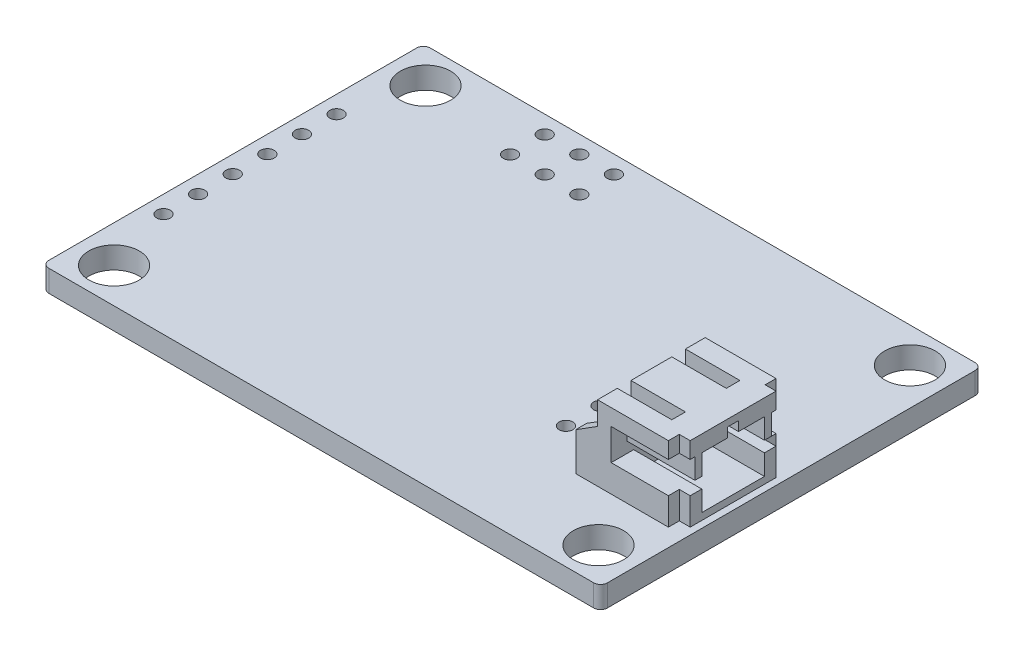
SolidWorks part; units mm, degrees
other "Sparkfun_board"
other "JST_connector"
ref_plane "Front Plane" through (0, 0, 0) normal (0, 0, 1) x (1, 0, 0)
ref_plane "Top Plane" through (0, 0, 0) normal (0, 1, 0) x (1, 0, 0)
ref_plane "Right Plane" through (0, 0, 0) normal (1, 0, 0) x (0, 0, -1)
sketch "dimension" plane through (0, 0, 0) normal (0, 1, 0) x (1, 0, 0)
  line L0 (0, 11.43) -> (0, -11.43) construction
  line L1 (-17.78, 11.43) -> (17.78, 11.43) construction
  line L2 (-17.78, 11.43) -> (-17.78, -11.43) construction
  line L3 (-17.78, -11.43) -> (17.78, -11.43) construction
  line L4 (17.78, 11.43) -> (17.78, -11.43) construction
  line L5 (-20.5, 14) -> (20.5, 14)
  line L6 (-20.5, 14) -> (-20.5, -14)
  line L7 (-20.5, -14) -> (20.5, -14)
  line L8 (20.5, 14) -> (20.5, -14)
  line L9 (-20.5, 0) -> (20.5, 0) construction
  circle A0 centre (-17.78, 11.43) radius 1.85
  circle A1 centre (17.78, 11.43) radius 1.85
  circle A2 centre (17.78, -11.43) radius 1.85
  circle A3 centre (-17.78, -11.43) radius 1.85
  dimension "D3" = 3.7
  dimension "D1" = 35.56
  dimension "D2" = 22.86
  dimension "D4" = 28
  dimension "D5" = 41
sketch "pin-holes" plane through (0, 0, 0) normal (0, 1, 0) x (1, 0, 0)
  line L1 (-20.5, 0) -> (20.5, 0) construction
  line L2 (-20.5, 14) -> (-20.5, -14) construction
  line L3 (-17.78, 11.43) -> (17.78, 11.43) construction
  line L4 (20.5, 14) -> (20.5, -14) construction
  line L6 (-20.5, -14) -> (20.5, -14) construction
  circle A0 centre (-19.23, 6.35) radius 0.5
  circle A1 centre (-19.23, 3.81) radius 0.5
  circle A2 centre (-19.23, 1.27) radius 0.5
  circle A3 centre (-19.23, -1.27) radius 0.5
  circle A4 centre (-19.23, -3.81) radius 0.5
  circle A5 centre (-19.23, -6.35) radius 0.5
  circle A6 centre (-10.3, 12.7) radius 0.5
  circle A7 centre (-7.76, 12.7) radius 0.5
  circle A8 centre (-5.22, 12.7) radius 0.5
  circle A9 centre (-7.76, 10.16) radius 0.5
  circle A10 centre (-5.22, 10.16) radius 0.5
  circle A11 centre (-10.3, 10.16) radius 0.5
  circle A12 centre (9, -2.5) radius 0.5
  circle A13 centre (9, -5.04) radius 0.5
  dimension "D3" = 1
  dimension "D2" = 2.54
  dimension "D6" = 10.2
  dimension "D7" = 2.54
  dimension "D8" = 2.54
  dimension "D9" = 2.54
  dimension "D10" = 11.5
  dimension "D11" = 11.5
  dimension "D12" = 1.27
  dimension "D1" = 6
  dimension "D4" = 3
  dimension "D5" = 2
sketch "Sketch1" plane through (0, 0, 0) normal (0, 1, 0) x (1, 0, 0)
  line L0 (-20.5, 14) -> (-20.5, -14) construction
  line L1 (-20.5, -14) -> (20.5, -14) construction
  line L2 (20.5, 14) -> (20.5, -14) construction
  line L3 (-20.5, 14) -> (20.5, 14) construction
  line L4 (-20.5, 14) -> (-20.5, -14)
  line L5 (-20.5, -14) -> (20.5, -14)
  line L6 (20.5, 14) -> (20.5, -14)
  line L7 (-20.5, 14) -> (20.5, 14)
  circle A0 centre (-17.78, 11.43) radius 1.85 construction
  circle A1 centre (-17.78, -11.43) radius 1.85 construction
  circle A2 centre (17.78, -11.43) radius 1.85 construction
  circle A3 centre (17.78, 11.43) radius 1.85 construction
  circle A4 centre (-17.78, 11.43) radius 1.85
  circle A5 centre (-17.78, -11.43) radius 1.85
  circle A6 centre (17.78, -11.43) radius 1.85
  circle A7 centre (17.78, 11.43) radius 1.85
extrude "board" add sketch "Sketch1" along normal blind 1.6
sketch "Sketch4" plane through (0, 0, 0) normal (0, 1, 0) x (1, 0, 0)
  circle A1 centre (-19.23, -6.35) radius 0.5
  circle A2 centre (-19.23, -6.35) radius 0.5
  circle A3 centre (-19.23, -3.81) radius 0.5
  circle A4 centre (-19.23, -3.81) radius 0.5
  circle A5 centre (-19.23, -1.27) radius 0.5
  circle A6 centre (-19.23, -1.27) radius 0.5
  circle A7 centre (-19.23, 1.27) radius 0.5
  circle A8 centre (-19.23, 1.27) radius 0.5
  circle A9 centre (-19.23, 3.81) radius 0.5
  circle A10 centre (-19.23, 3.81) radius 0.5
  circle A11 centre (-19.23, 6.35) radius 0.5
  circle A12 centre (-19.23, 6.35) radius 0.5
  circle A13 centre (-5.22, 10.16) radius 0.5
  circle A14 centre (-5.22, 10.16) radius 0.5
  circle A15 centre (-7.76, 10.16) radius 0.5
  circle A16 centre (-7.76, 10.16) radius 0.5
  circle A17 centre (-5.22, 12.7) radius 0.5
  circle A18 centre (-5.22, 12.7) radius 0.5
  circle A19 centre (-7.76, 12.7) radius 0.5
  circle A20 centre (-7.76, 12.7) radius 0.5
  circle A21 centre (-10.3, 12.7) radius 0.5
  circle A22 centre (-10.3, 12.7) radius 0.5
  circle A23 centre (9, -5.04) radius 0.5
  circle A24 centre (9, -5.04) radius 0.5
  circle A25 centre (9, -2.5) radius 0.5
  circle A26 centre (9, -2.5) radius 0.5
  circle A27 centre (-10.3, 10.16) radius 0.5
  circle A28 centre (-10.3, 10.16) radius 0.5
  dimension "D1" = 0
  dimension "D2" = 0
  dimension "D3" = 0
  dimension "D4" = 0
  dimension "D5" = 0
  dimension "D6" = 0
  dimension "D7" = 0
  dimension "D8" = 0
  dimension "D9" = 0
  dimension "D10" = 0
  dimension "D11" = 0
  dimension "D12" = 0
  dimension "D13" = 0
  dimension "D14" = 0
extrude "holes" cut sketch "Sketch4" along normal through all
fillet "Fillet1" radius 0.5 4 edges at (20.5, 0.8, -14) (20.5, 0.8, 14) (-20.5, 0.8, 14) (-20.5, 0.8, -14)
sketch "Sketch5" plane through (0, 1.6, 0) normal (0, 1, 0) x (1, 0, 0)
  line L0 (20.5, -13.5) -> (20.5, 13.5) construction
  line L1 (14, -3.77) -> (20, -3.77)
  line L2 (14, -3.77) -> (14, -7.72)
  line L3 (14, -7.72) -> (20, -7.72)
  line L4 (20, -3.77) -> (20, -7.72)
  line L5 (9, -2.5) -> (9, -5.04) construction
  line L6 (9, -3.77) -> (14, -3.77) construction
  dimension "D1" = 3.95
  dimension "D2" = 6
  dimension "D3" = 0.5
extrude "Boss-Extrude2" add sketch "Sketch5" along normal blind 5.5 separate body
sketch "Sketch8" plane through (0, 0, 7.72) normal (0, 0, 1) x (1, 0, 0)
  line L0 (12.4, 1.6) -> (12.4, 4.4)
  line L1 (9, 1.6) -> (14, 1.6) construction
  line L2 (12.4, 4.4) -> (14, 5.4)
  line L3 (14, 7.1) -> (14, 1.6) construction
  line L4 (14, 5.4) -> (14, 1.6)
  line L5 (14, 1.6) -> (12.4, 1.6)
  dimension "D1" = 7.6
  dimension "D2" = 3.8
  dimension "D3" = 2.8
extrude "Boss-Extrude3" add sketch "Sketch8" against normal blind 0.8
sketch "Sketch6" plane through (20, 0, 0) normal (1, 0, 0) x (0, 0, -1)
  line L5 (-6.07, 5.9) -> (-4.17, 5.9)
  line L6 (-6.07, 5.9) -> (-6.07, 4.4)
  line L7 (-6.07, 2.1) -> (-3.77, 2.1)
  line L9 (-7.72, 7.1) -> (-3.77, 7.1) construction
  line L11 (-7.72, 1.6) -> (-3.77, 1.6) construction
  line L12 (-3.77, 2.1) -> (-3.77, 6.6)
  line L13 (-4.17, 5.9) -> (-4.17, 6.6)
  line L14 (-4.17, 6.6) -> (-3.77, 6.6)
  line L17 (-6.07, 3.6) -> (-7.72, 3.6)
  line L18 (-7.72, 7.1) -> (-7.72, 1.6) construction
  line L19 (-7.72, 3.6) -> (-7.72, 5.9)
  line L20 (-7.72, 5.9) -> (-6.57, 5.9)
  line L21 (-6.57, 5.9) -> (-6.57, 4.4)
  line L22 (-6.57, 4.4) -> (-6.07, 4.4)
  line L23 (-6.07, 3.6) -> (-6.07, 2.1)
  point P13 (-3.77, 2.1)
  point P30 (-3.77, 6.6)
  dimension "D1" = 0.5
  dimension "D2" = 1.2
  dimension "D3" = 0.5
  dimension "D4" = 0.5
  dimension "D5" = 2
  dimension "D6" = 0.4
  dimension "D7" = 2.3
  dimension "D8" = 0.8
extrude "Cut-Extrude2" cut sketch "Sketch6" against normal blind 5
sketch "Sketch7" plane through (0, 7.1, 0) normal (0, 1, 0) x (1, 0, 0)
  line L1 (14, -3.77) -> (14, -7.72) construction
  line L5 (9, -3.77) -> (20.8509, -3.77) construction
  line L6 (18, -6.27) -> (18, -5.27)
  line L7 (14, -5.27) -> (18, -5.27)
  line L8 (14, -6.27) -> (14, -5.27)
  line L9 (14, -6.27) -> (18, -6.27)
  dimension "D1" = 1
  dimension "D2" = 4
  dimension "D3" = 2.5
extrude "Cut-Extrude3" cut sketch "Sketch7" against normal blind 1
sketch "Sketch9" plane through (0, 7.1, 0) normal (0, 1, 0) x (1, 0, 0)
  line L1 (20, -7.72) -> (19.2, -7.72)
  line L2 (20, -7.72) -> (20, -6.92)
  line L3 (20, -6.92) -> (19.2, -6.92)
  line L4 (19.2, -7.72) -> (19.2, -6.92)
  dimension "D1" = 0.8
extrude "Cut-Extrude4" cut sketch "Sketch9" against normal through all
mirror "Mirror1" about plane through (14, 7.1, 3.77) normal (0, 0, 1) of bodies 107
